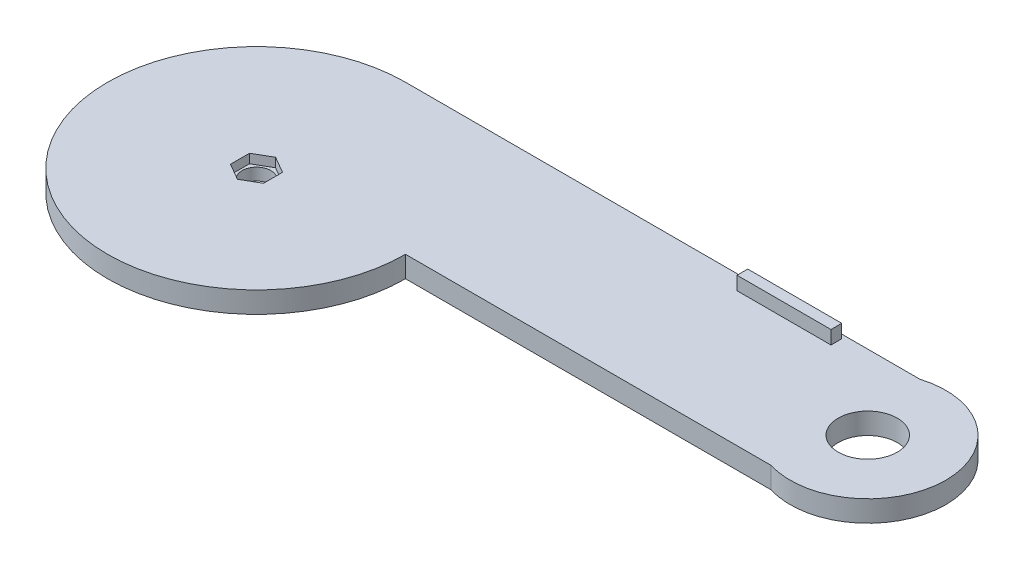
SolidWorks part; units mm, degrees
ref_plane "Front Plane" through (0, 0, 0) normal (0, 0, 1) x (1, 0, 0)
ref_plane "Top Plane" through (0, 0, 0) normal (0, 1, 0) x (1, 0, 0)
ref_plane "Right Plane" through (0, 0, 0) normal (1, 0, 0) x (0, 0, -1)
sketch "Эскиз1" plane through (0, 0, 0) normal (0, 1, 0) x (1, 0, 0)
  line L0 (0, 55.5) -> (200, 55.5)
  line L1 (200, 55.5) -> (200, 0)
  line L2 (200, 0) -> (0, 0)
  circle A0 centre (0, 0) radius 55.5
  circle A1 centre (200, 27.75) radius 27.75
  circle A2 centre (200, 27.75) radius 29
  dimension "D1" = 111
  dimension "D2" = 200
extrude "Бобышка-Вытянуть1" add sketch "Эскиз1" along normal blind 7.9
sketch "Эскиз2" plane through (0, 7.9, 0) normal (0, 1, 0) x (1, 0, 0)
  circle A3 centre (0, 0) radius 5.341
  point P0 (0, 0)
  point P288 (0, 0)
sketch "Эскиз20" plane through (0, 7.9, 0) normal (0, 1, 0) x (1, 0, 0)
  line L14 (129, 49.9801) -> (164, 49.9801)
  line L15 (129, 49.9801) -> (129, 53.9801)
  line L16 (129, 53.9801) -> (164, 53.9801)
  line L17 (164, 49.9801) -> (164, 53.9801)
  dimension "D10" = 35
  dimension "D12" = 4
  dimension "D15" = 129
extrude "Бобышка-Вытянуть10" add sketch "Эскиз20" along normal blind 5
sketch "Эскиз21" plane through (0, 7.9, 0) normal (0, 1, 0) x (1, 0, 0)
  circle A0 centre (199.92, 27.7499) radius 11
extrude "Вырез-Вытянуть2" cut sketch "Эскиз21" against normal through all
extrude "Вырез-Вытянуть3" cut sketch "Эскиз2" against normal blind 10
sketch "Эскиз22" plane through (0, 7.9, 0) normal (0, 1, 0) x (1, 0, 0)
  line L1 (0, 7.1) -> (-6.1488, 3.55)
  line L2 (-6.1488, 3.55) -> (-6.1488, -3.55)
  line L3 (-6.1488, -3.55) -> (0, -7.1)
  line L4 (0, -7.1) -> (6.1488, -3.55)
  line L5 (6.1488, -3.55) -> (6.1488, 3.55)
  line L6 (6.1488, 3.55) -> (0, 7.1)
  circle A0 centre (0, 0) radius 6.1488 construction
  dimension "D1" = 14.2
extrude "Вырез-Вытянуть4" cut sketch "Эскиз22" against normal blind 3.4
